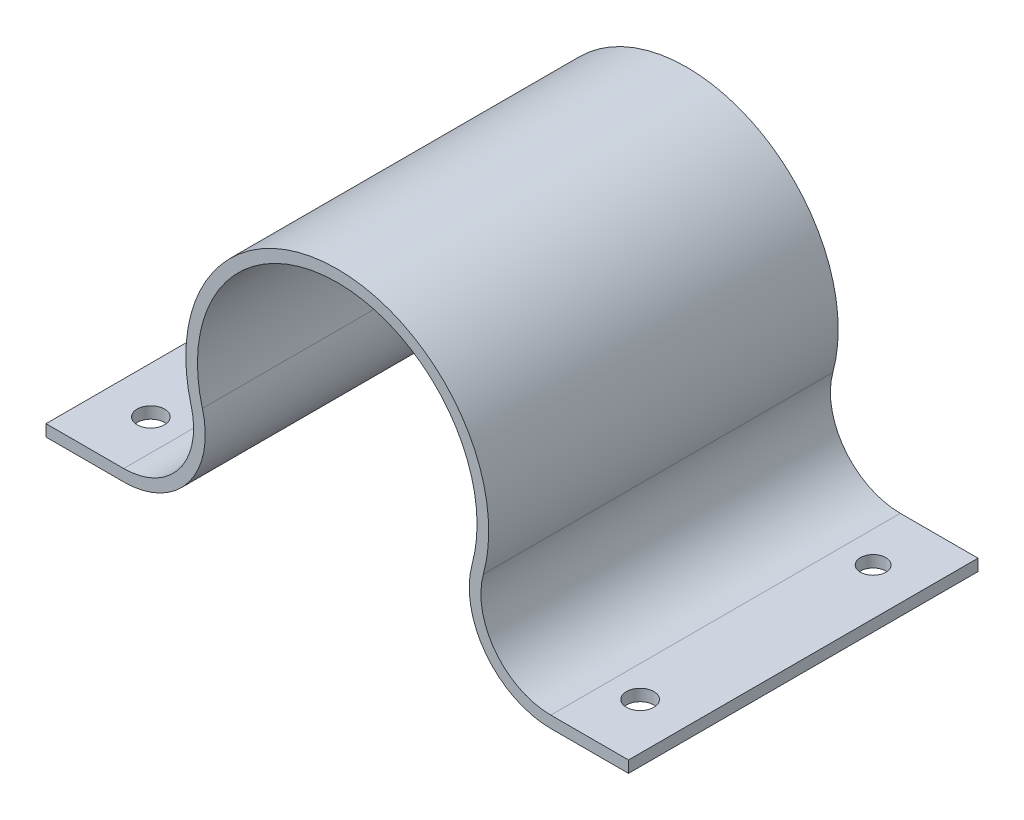
SolidWorks part; units mm, degrees
ref_plane "Front Plane" through (0, 0, 0) normal (0, 0, 1) x (1, 0, 0)
ref_plane "Top Plane" through (0, 0, 0) normal (0, 1, 0) x (1, 0, 0)
ref_plane "Right Plane" through (0, 0, 0) normal (1, 0, 0) x (0, 0, -1)
sketch "Sketch1" plane through (0, 0, 0) normal (0, 0, 1) x (1, 0, 0)
  line L0 (-25, -12) -> (-18.3303, -12)
  line L1 (0, 0) -> (0, -12) construction
  line L2 (18.3303, -12) -> (25, -12)
  line L3 (-25, -11) -> (-18.3303, -11)
  line L4 (18.3303, -11) -> (25, -11)
  line L5 (-25, -12) -> (-25, -11)
  line L6 (25, -12) -> (25, -11)
  arc A0 (11.577, -3.1579) -> (-11.577, -3.1579) centre (0, 0) ccw
  arc A1 (-18.3303, -12) -> (-11.577, -3.1579) centre (-18.3303, -5) ccw
  arc A2 (18.3303, -12) -> (11.577, -3.1579) centre (18.3303, -5) cw
  arc A3 (-18.3303, -11) -> (-12.5418, -3.4211) centre (-18.3303, -5) ccw
  arc A4 (12.5418, -3.4211) -> (-12.5418, -3.4211) centre (0, 0) ccw
  arc A5 (18.3303, -11) -> (12.5418, -3.4211) centre (18.3303, -5) cw
  dimension "D1" = 24
  dimension "D3" = 7
  dimension "D2" = 50
  dimension "D4" = 1
extrude "Boss-Extrude1" add sketch "Sketch1" along normal blind 30
sketch "Sketch2" plane through (0, -11, 0) normal (0, 1, 0) x (1, 0, 0)
  line L0 (25, 0) -> (18.3303, 0) construction
  line L1 (25, -30) -> (25, 0) construction
  line L2 (25, -30) -> (18.3303, -30) construction
  circle A0 centre (21, -5) radius 1.0895
  circle A1 centre (21, -25) radius 1.174
  point P8 (21.6652, -30)
  dimension "D1" = 5
  dimension "D2" = 4
  dimension "D3" = 5
  dimension "D4" = 4
extrude "Cut-Extrude1" cut sketch "Sketch2" against normal blind 15
mirror "Mirror1" about plane through (0, 0, 0) normal (1, 0, 0) of "Cut-Extrude1"
